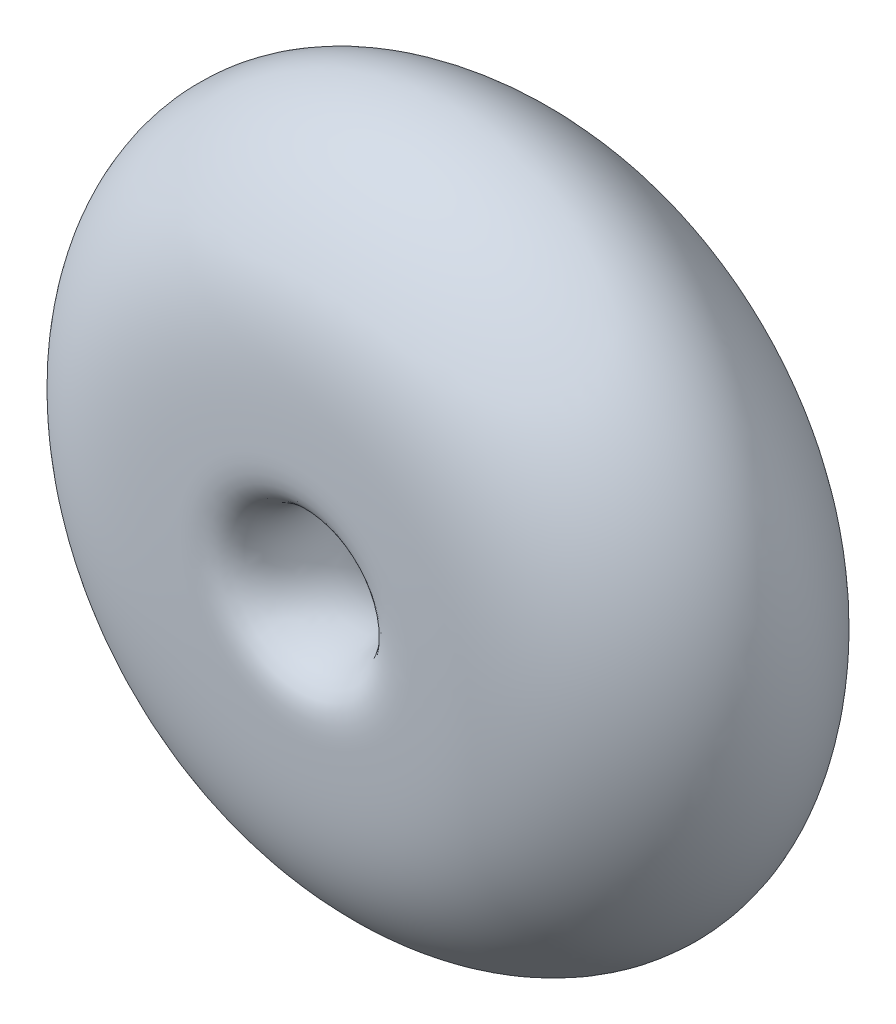
SolidWorks part; units mm, degrees
ref_plane "Front Plane" through (0, 0, 0) normal (0, 0, 1) x (1, 0, 0)
ref_plane "Top Plane" through (0, 0, 0) normal (0, 1, 0) x (1, 0, 0)
ref_plane "Right Plane" through (0, 0, 0) normal (1, 0, 0) x (0, 0, -1)
sketch "Sketch1" plane through (0, 0, 0) normal (0, 1, 0) x (1, 0, 0)
  line L0 (-17.2487, 66.5603) -> (-17.2487, -10.5022) construction
  spline S0 degree 3 poles (16.0601, 0.204) (-7.5747, -0.4494) (-6.6778, 36.6985) (29.0545, 30.5651) (20.2498, 75.586) (70.5881, 37.6222) (40.7718, 0.9477) (16.0601, 0.204) (-7.5747, -0.4494) (-6.6778, 36.6985) knots -0.413607 -0.201788 -0.046728 0 0.14665 0.279908 0.400677 0.586393 0.798212 0.953272 1 1.14665 1.279908 1.400677 only from (0, 1.0433) to (0, 1.0433)
revolve "Revolve1" add sketch "Sketch1" angle 360 about L0
